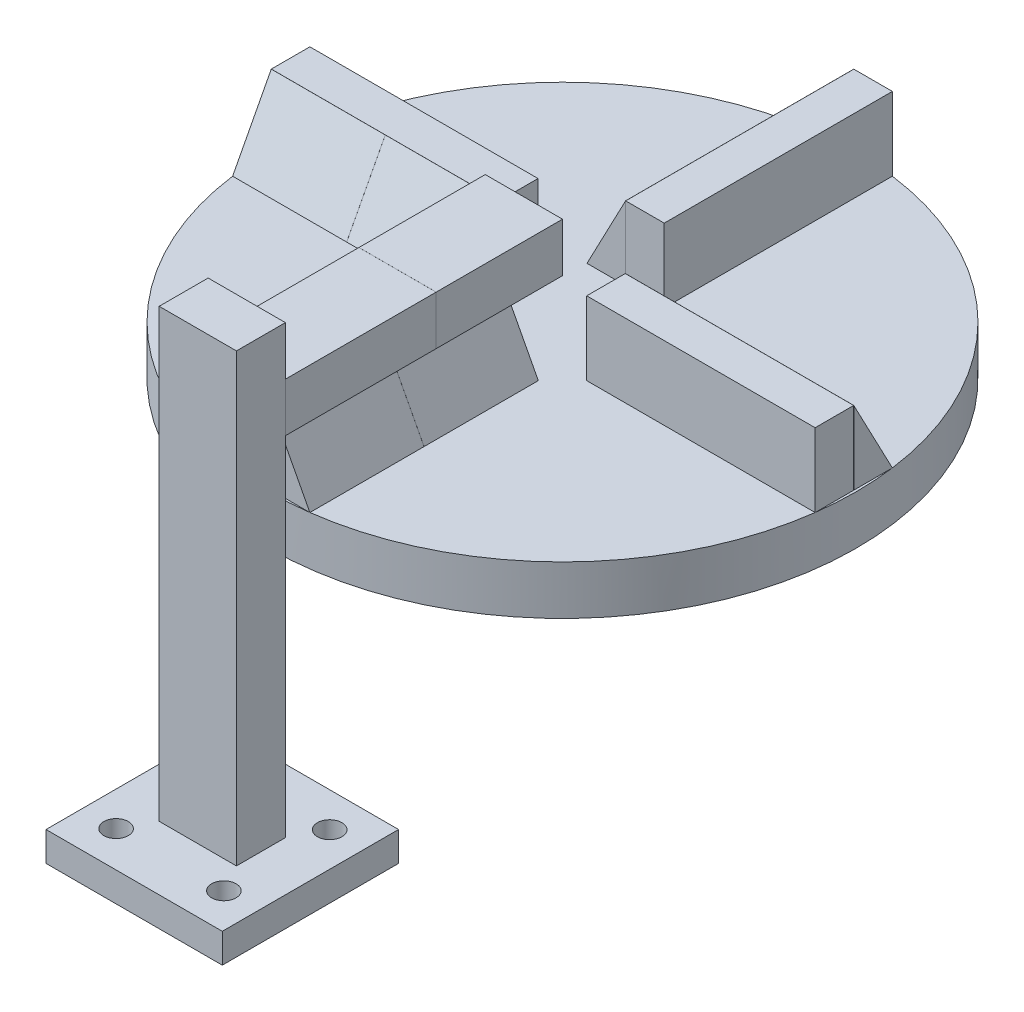
SolidWorks part; units mm, degrees
ref_plane "Front Plane" through (0, 0, 0) normal (0, 0, 1) x (1, 0, 0)
ref_plane "Top Plane" through (0, 0, 0) normal (0, 1, 0) x (1, 0, 0)
ref_plane "Right Plane" through (0, 0, 0) normal (1, 0, 0) x (0, 0, -1)
sketch "Sketch1" plane through (0, 0, 0) normal (0, 1, 0) x (1, 0, 0)
  circle A0 centre (0, 0) radius 60
extrude "Boss-Extrude1" add sketch "Sketch1" along normal blind 10
sketch "Sketch2" plane through (0, 0, 0) normal (0, -1, 0) x (1, 0, 0)
  circle A0 centre (0, 0) radius 1.5
extrude "Cut-Extrude1" cut sketch "Sketch2" against normal blind 4
sketch "Sketch3" plane through (0, 10, 0) normal (0, 1, 0) x (1, 0, 0)
  line L0 (0, 60) -> (0, -60) construction
  line L1 (-7.8876, -12.8285) -> (7.8876, -12.8285)
  line L2 (-7.8876, -12.8285) -> (-7.8876, -59.4793)
  line L3 (-7.8876, -59.4793) -> (7.8876, -59.4793)
  line L4 (7.8876, -12.8285) -> (7.8876, -59.4793)
  line L5 (-12.8285, 7.8876) -> (-59.4793, 7.8876)
  line L6 (-12.8285, 7.8876) -> (-12.8285, -7.8876)
  line L7 (-12.8285, -7.8876) -> (-59.4793, -7.8876)
  line L8 (-59.4793, 7.8876) -> (-59.4793, -7.8876)
  line L9 (7.8876, 12.8285) -> (7.8876, 59.4793)
  line L10 (7.8876, 12.8285) -> (-7.8876, 12.8285)
  line L11 (-7.8876, 12.8285) -> (-7.8876, 59.4793)
  line L12 (7.8876, 59.4793) -> (-7.8876, 59.4793)
  line L13 (12.8285, -7.8876) -> (59.4793, -7.8876)
  line L14 (12.8285, -7.8876) -> (12.8285, 7.8876)
  line L15 (12.8285, 7.8876) -> (59.4793, 7.8876)
  line L16 (59.4793, -7.8876) -> (59.4793, 7.8876)
  circle A0 centre (0, 0) radius 60 construction
  dimension "D1" = 4
extrude "Boss-Extrude2" add sketch "Sketch3" along normal blind 15
sketch "Sketch4" plane through (0, 0, 59.4793) normal (0, 0, 1) x (1, 0, 0)
  line L0 (0, 25) -> (7.8876, 10)
  line L1 (-7.8876, 25) -> (7.8876, 25) construction
  line L2 (7.8876, 10) -> (7.8876, 25)
  line L3 (7.8876, 25) -> (0, 25)
extrude "Cut-Extrude2" cut sketch "Sketch4" against normal through all
sketch "Sketch5" plane through (0, 0, 59.4793) normal (0, 0, 1) x (1, 0, 0)
  line L0 (7.8876, 10) -> (-7.8876, 10) construction
  line L2 (0, 25) -> (-0.01, 25)
  line L3 (0, 25) -> (0, 10)
  line L4 (0, 10) -> (-0.01, 10)
  line L5 (-0.01, 25) -> (-0.01, 10)
  dimension "D1" = 0.01
extrude "Cut-Extrude3" cut sketch "Sketch5" against normal through all
sketch "Sketch6" plane through (10.2984, 5.4154, 0) normal (0.8851, 0.4654, 0) x (0, 0, -1)
  line L0 (-12.8285, 22.1273) -> (-59.4793, 22.1273) construction
  line L1 (-36.1539, 22.1273) -> (-36.1639, 22.1273)
  line L2 (-36.1539, 22.1273) -> (-36.1539, 5.1798)
  line L3 (-36.1539, 5.1798) -> (-36.1639, 5.1798)
  line L4 (-36.1639, 22.1273) -> (-36.1639, 5.1798)
  line L5 (-59.4793, 5.1798) -> (-12.8285, 5.1798) construction
  dimension "D1" = 0.01
extrude "Cut-Extrude4" cut sketch "Sketch6" against normal blind 7
sketch "Sketch8" plane through (59.4793, 0, 0) normal (1, 0, 0) x (0, 0, -1)
  line L0 (0, 25) -> (7.8876, 10)
  line L1 (-7.8876, 25) -> (7.8876, 25) construction
  line L2 (7.8876, 10) -> (7.8876, 25)
  line L3 (7.8876, 25) -> (0, 25)
extrude "Cut-Extrude5" cut sketch "Sketch8" against normal through all
sketch "Sketch9" plane through (59.4793, 0, 0) normal (1, 0, 0) x (0, 0, -1)
  line L0 (7.8876, 10) -> (-7.8876, 10) construction
  line L1 (0, 25) -> (-0.01, 25)
  line L2 (0, 25) -> (0, 10)
  line L3 (0, 10) -> (-0.01, 10)
  line L4 (-0.01, 25) -> (-0.01, 10)
  dimension "D1" = 0.01
extrude "Cut-Extrude6" cut sketch "Sketch9" against normal through all
sketch "Sketch12" plane through (0, 0, 59.4793) normal (0, 0, 1) x (1, 0, 0)
  line L1 (-7.8876, 25) -> (-7.2172, 25)
  line L2 (-7.8876, 25) -> (-7.8876, 26.086)
  line L3 (-7.8876, 26.086) -> (-7.2172, 26.086)
  line L4 (-7.2172, 25) -> (-7.2172, 26.086)
  line L5 (-7.8876, 26.086) -> (7.8876, 26.086)
  line L6 (-7.8876, 26.086) -> (-7.8876, 36.086)
  line L7 (-7.8876, 36.086) -> (7.8876, 36.086)
  line L8 (7.8876, 26.086) -> (7.8876, 36.086)
  dimension "D1" = 10
extrude "Boss-Extrude3" add sketch "Sketch12" against normal up to surface (51.5916 mm away) separate body contours L6 L5 L8 L7 up to face at (36.1539, 17.5, 7.8876)
sketch "Sketch13" plane through (7.8876, 0, 0) normal (1, 0, 0) x (0, 0, -1)
  line L0 (-7.8876, 36.086) -> (-59.4793, 36.086) construction
  line L1 (-33.6835, 36.086) -> (-33.6935, 36.086)
  line L2 (-33.6835, 36.086) -> (-33.6835, 26.086)
  line L3 (-33.6835, 26.086) -> (-33.6935, 26.086)
  line L4 (-33.6935, 36.086) -> (-33.6935, 26.086)
  line L5 (-7.8876, 26.086) -> (-59.4793, 26.086) construction
  dimension "D1" = 0.01
sketch "Sketch14" plane through (0, 0, 59.4793) normal (0, 0, 1) x (1, 0, 0)
  line L4 (7.8876, 36.086) -> (-7.8876, 36.086)
  line L5 (-7.8876, 36.086) -> (-7.8876, 26.086)
  line L6 (-7.8876, 26.086) -> (7.8876, 26.086)
  line L7 (7.8876, 26.086) -> (7.8876, 36.086)
  line L8 (7.8876, 36.086) -> (-7.8876, 36.086)
  line L9 (-7.8876, 36.086) -> (-7.8876, 26.086)
  line L10 (-7.8876, 26.086) -> (7.8876, 26.086)
  line L11 (7.8876, 26.086) -> (7.8876, 36.086)
  dimension "D1" = 0
extrude "Boss-Extrude4" add sketch "Sketch14" along normal blind 5
extrude "Cut-Extrude9" cut sketch "Sketch13" against normal through all
sketch "Sketch15" plane through (0, 0, 64.4793) normal (0, 0, 1) x (1, 0, 0)
  line L4 (7.8876, 26.086) -> (7.8876, 36.086)
  line L5 (7.8876, 36.086) -> (-7.8876, 36.086)
  line L6 (-7.8876, 36.086) -> (-7.8876, 26.086)
  line L7 (-7.8876, 26.086) -> (7.8876, 26.086)
  line L8 (7.8876, 26.086) -> (7.8876, 36.086)
  line L9 (7.8876, 36.086) -> (-7.8876, 36.086)
  line L10 (-7.8876, 36.086) -> (-7.8876, 26.086)
  line L11 (-7.8876, 26.086) -> (7.8876, 26.086)
  dimension "D1" = 0
extrude "Boss-Extrude5" add sketch "Sketch15" along normal blind 10
sketch "Sketch16" plane through (0, 36.086, 0) normal (0, 1, 0) x (1, 0, 0)
  line L0 (7.8876, -33.6935) -> (7.8876, -74.4793) construction
  line L1 (-7.8876, -74.4793) -> (7.8876, -74.4793)
  line L2 (-7.8876, -74.4793) -> (-7.8876, -64.4793)
  line L3 (-7.8876, -64.4793) -> (7.8876, -64.4793)
  line L4 (7.8876, -74.4793) -> (7.8876, -64.4793)
  dimension "D1" = 10
extrude "Boss-Extrude6" add sketch "Sketch16" along normal blind 10 and the other way blind 54
sketch "Sketch17" plane through (7.8876, 0, 0) normal (1, 0, 0) x (0, 0, -1)
  line L0 (-33.6935, 26.086) -> (-64.4793, 26.086) construction
  line L1 (-64.4793, 36.086) -> (-64.4693, 36.086)
  line L2 (-64.4793, 36.086) -> (-64.4793, 26.086)
  line L3 (-64.4793, 26.086) -> (-64.4693, 26.086)
  line L4 (-64.4693, 36.086) -> (-64.4693, 26.086)
  dimension "D1" = 0.01
extrude "Cut-Extrude10" cut sketch "Sketch17" against normal through all
sketch "Sketch18" plane through (0, 0, -59.4793) normal (0, 0, -1) x (-1, 0, 0)
  line L1 (-7.8876, 10) -> (7.8876, 10)
  line L2 (-7.8876, 10) -> (-7.8876, 25)
  line L3 (-7.8876, 25) -> (7.8876, 25)
  line L4 (7.8876, 10) -> (7.8876, 25)
extrude "Cut-Extrude11" cut sketch "Sketch18" against normal up to surface (46.6508 mm away) up to face at (-3.9488, 17.5, -12.8285)
sketch "Sketch19" plane through (-59.4793, 0, 0) normal (-1, 0, 0) x (0, 0, 1)
  line L3 (-7.8876, 10) -> (0, 10)
  line L4 (7.8876, 25) -> (0.01, 25)
  line L5 (0.01, 25) -> (0.01, 10)
  line L6 (0.01, 10) -> (7.8876, 10)
  line L7 (7.8876, 10) -> (7.8876, 25)
  line L8 (7.8876, 25) -> (0.01, 25)
  line L9 (0.01, 25) -> (0.01, 10)
  line L10 (0.01, 10) -> (7.8876, 10)
  line L11 (7.8876, 10) -> (7.8876, 25)
  line L12 (0, 10) -> (0, 25)
  line L13 (0, 25) -> (-7.8876, 10)
  line L14 (-7.8876, 10) -> (0, 10)
  line L15 (0, 10) -> (0, 25)
  line L16 (0, 25) -> (-7.8876, 10)
  dimension "D1" = 0
  dimension "D2" = 0
extrude "Cut-Extrude12" cut sketch "Sketch19" against normal up to surface (46.6508 mm away) contours L14 L15 L16 | L8 L9 L10 L11 up to face at (-12.8285, 17.5, 3.9488)
sketch "Sketch20" plane through (0, 10, 0) normal (0, 1, 0) x (1, 0, 0)
  line L0 (-12.8876, 7.8876) -> (-59.4793, 7.8876)
  line L2 (12.8285, 7.8876) -> (12.8285, -7.8876)
  line L4 (-59.4793, 7.8876) -> (-59.4793, -7.8876)
  line L5 (7.8876, -7.8876) -> (-7.8876, -7.8876)
  line L9 (-59.4793, -7.8876) -> (-12.8876, -7.8876)
  line L10 (-59.4793, -7.8876) -> (-59.4793, 7.8876)
  line L11 (-59.4793, 7.8876) -> (-12.8876, 7.8876)
  line L12 (-12.8876, -7.8876) -> (-12.8876, 7.8876)
  line L13 (-7.8876, 12.8876) -> (7.8876, 12.8876)
  line L18 (-7.8876, 12.8876) -> (7.8876, 12.8876)
  line L19 (-7.8876, 12.8876) -> (-7.8876, 59.4793)
  line L20 (-7.8876, 59.4793) -> (7.8876, 59.4793)
  line L21 (7.8876, 12.8876) -> (7.8876, 59.4793)
  arc A0 (59.4793, 7.8876) -> (-7.8876, -59.4793) centre (0, 0) ccw construction
extrude "Boss-Extrude12" add sketch "Sketch20" along normal up to surface (15 mm away) up to face at (36.1539, 25, 3.9488)
sketch "Sketch21" plane through (0, 0, -59.4793) normal (0, 0, -1) x (-1, 0, 0)
  line L0 (0, 25) -> (7.8876, 10)
  line L1 (-7.8876, 25) -> (7.8876, 25) construction
  line L2 (7.8876, 10) -> (7.8876, 25)
  line L3 (7.8876, 25) -> (1.0004, 25)
  line L4 (1.0004, 25) -> (0, 25)
extrude "Cut-Extrude13" cut sketch "Sketch21" against normal up to surface (46.5916 mm away) up to face at (0, 17.5, -12.8876)
sketch "Sketch22" plane through (-59.4793, 0, 0) normal (-1, 0, 0) x (0, 0, 1)
  line L0 (0, 25) -> (7.8876, 10)
  line L1 (7.8876, 25) -> (-7.8876, 25) construction
  line L2 (7.8876, 10) -> (7.8876, 25)
  line L3 (7.8876, 25) -> (0, 25)
extrude "Cut-Extrude14" cut sketch "Sketch22" against normal up to surface (51.5916 mm away) up to face at (-7.8876, 17.5, 36.1539)
sketch "Sketch23" plane through (-59.4793, 0, 0) normal (-1, 0, 0) x (0, 0, 1)
  line L0 (-7.8876, 10) -> (7.8876, 10) construction
  line L1 (0, 25) -> (-0.01, 25)
  line L2 (0, 25) -> (0, 10)
  line L3 (0, 10) -> (-0.01, 10)
  line L4 (-0.01, 25) -> (-0.01, 10)
  dimension "D1" = 0.01
extrude "Cut-Extrude15" cut sketch "Sketch23" against normal blind 48
sketch "Sketch24" plane through (0, 0, -59.4793) normal (0, 0, -1) x (-1, 0, 0)
  line L0 (7.8876, 10) -> (-7.8876, 10) construction
  line L1 (0, 25) -> (-0.01, 25)
  line L2 (0, 25) -> (0, 10)
  line L3 (0, 10) -> (-0.01, 10)
  line L4 (-0.01, 25) -> (-0.01, 10)
  dimension "D1" = 0.01
extrude "Cut-Extrude16" cut sketch "Sketch24" against normal blind 48
sketch "Sketch26" plane through (0, 5.4154, 10.2984) normal (0, 0.4654, 0.8851) x (1, 0, 0)
  line L0 (-59.4793, 22.1273) -> (-12.8876, 22.1273) construction
  line L1 (-36.1835, 22.1273) -> (-36.1935, 22.1273)
  line L2 (-36.1835, 22.1273) -> (-36.1835, 5.1798)
  line L3 (-36.1835, 5.1798) -> (-36.1935, 5.1798)
  line L4 (-36.1935, 22.1273) -> (-36.1935, 5.1798)
  line L5 (-59.4793, 5.1798) -> (-12.8876, 5.1798) construction
  dimension "D1" = 0.01
extrude "Cut-Extrude18" cut sketch "Sketch26" against normal blind 5
sketch "Sketch28" plane through (0, 5.4154, -10.2984) normal (0, 0.4654, -0.8851) x (-1, 0, 0)
  line L0 (-59.4793, 22.1273) -> (-12.8285, 22.1273) construction
  line L1 (-36.1539, 22.1273) -> (-36.1639, 22.1273)
  line L2 (-36.1539, 22.1273) -> (-36.1539, 5.1798)
  line L3 (-36.1539, 5.1798) -> (-36.1639, 5.1798)
  line L4 (-36.1639, 22.1273) -> (-36.1639, 5.1798)
  line L5 (-59.4793, 5.1798) -> (-12.8285, 5.1798) construction
  dimension "D1" = 0.01
extrude "Cut-Extrude20" cut sketch "Sketch28" against normal blind 6
sketch "Sketch29" plane through (-10.2984, 5.4154, 0) normal (-0.8851, 0.4654, 0) x (0, 0, 1)
  line L0 (-12.8876, 22.1273) -> (-59.4793, 22.1273) construction
  line L1 (-36.1835, 22.1273) -> (-36.1935, 22.1273)
  line L2 (-36.1835, 22.1273) -> (-36.1835, 5.1798)
  line L3 (-36.1835, 5.1798) -> (-36.1935, 5.1798)
  line L4 (-36.1935, 22.1273) -> (-36.1935, 5.1798)
  line L5 (-12.8876, 5.1798) -> (-59.4793, 5.1798) construction
  dimension "D1" = 0.01
extrude "Cut-Extrude21" cut sketch "Sketch29" against normal blind 6
sketch "Sketch30" plane through (0, -17.914, 0) normal (0, -1, 0) x (1, 0, 0)
  line L4 (-7.8876, 74.4793) -> (-7.8876, 64.4793)
  line L5 (-7.8876, 64.4793) -> (7.8876, 64.4793)
  line L6 (7.8876, 64.4793) -> (7.8876, 74.4793)
  line L7 (7.8876, 74.4793) -> (-7.8876, 74.4793)
  line L8 (-7.8876, 74.4793) -> (-7.8876, 64.4793)
  line L9 (-7.8876, 64.4793) -> (7.8876, 64.4793)
  line L10 (7.8876, 64.4793) -> (7.8876, 74.4793)
  line L11 (7.8876, 74.4793) -> (-7.8876, 74.4793)
  dimension "D1" = 0
extrude "Boss-Extrude13" add sketch "Sketch30" along normal blind 33.09
sketch "Sketch31" plane through (0, -51.004, 0) normal (0, -1, 0) x (1, 0, 0)
  line L0 (7.8876, 69.4793) -> (-7.8876, 69.4793) construction
  line L1 (7.8876, 64.4793) -> (7.8876, 74.4793) construction
  line L2 (-7.8876, 74.4793) -> (-7.8876, 64.4793) construction
  line L4 (-18, 87.4793) -> (18, 87.4793)
  line L5 (-18, 87.4793) -> (-18, 51.4793)
  line L6 (-18, 51.4793) -> (18, 51.4793)
  line L7 (18, 87.4793) -> (18, 51.4793)
  line L8 (-18, 87.4793) -> (18, 51.4793) construction
  line L9 (-18, 51.4793) -> (18, 87.4793) construction
  point P6 (0, 69.4793)
  dimension "D1" = 36
  dimension "D2" = 36
extrude "Boss-Extrude14" add sketch "Sketch31" against normal blind 6
sketch "Sketch32" plane through (0, -51.004, 0) normal (0, -1, 0) x (1, 0, 0)
  line L0 (0, 87.4793) -> (0, 51.2296) construction
  line L1 (18, 87.4793) -> (-18, 87.4793) construction
  line L2 (0, 51.2296) -> (0, 69.3544) construction
  line L3 (0, 69.3544) -> (18, 69.3544) construction
  circle A0 centre (11.0017, 80.1596) radius 2.5
  circle A1 centre (11.0017, 58.5492) radius 2.5
  circle A2 centre (-11.0017, 58.5492) radius 2.5
  circle A3 centre (-11.0017, 80.1596) radius 2.5
extrude "Cut-Extrude22" cut sketch "Sketch32" against normal blind 6
